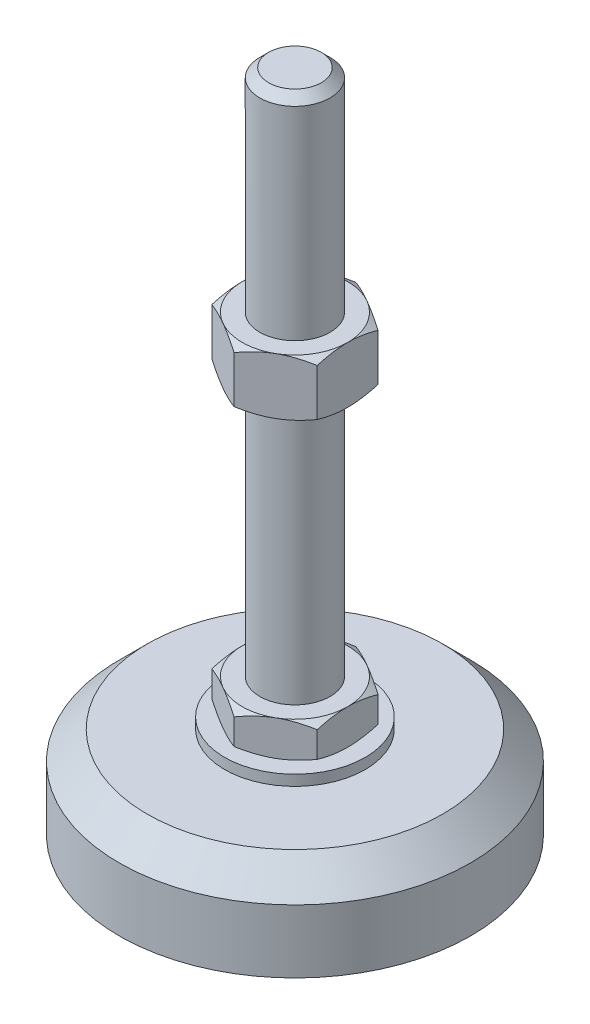
SolidWorks part; units mm, degrees
ref_plane "Спереди" through (0, 0, 0) normal (0, 0, 1) x (1, 0, 0)
ref_plane "Сверху" through (0, 0, 0) normal (0, 1, 0) x (1, 0, 0)
ref_plane "Справа" through (0, 0, 0) normal (1, 0, 0) x (0, 0, -1)
sketch "Эскиз1" plane through (0, 0, 0) normal (0, 0, 1) x (1, 0, 0)
  line L0 (0, 0) -> (-50, 0)
  line L3 (-50, 0) -> (-50, 18)
  line L5 (-20, 29) -> (-10, 29)
  line L12 (-10, 39) -> (-10, 186.5)
  line L13 (-10, 186.5) -> (-7.5, 189)
  line L14 (-7.5, 189) -> (0, 189)
  line L15 (0, 189) -> (0, 0) construction
  line L16 (-10, 29) -> (0, 29) construction
  line L17 (0, 0) -> (0, 189)
  line L18 (0, 0) -> (0, -7.9595) construction
  line L19 (-10, 39) -> (-10, 29)
  line L20 (-20, 29) -> (-20, 26)
  line L21 (-20, 26) -> (-42, 26)
  line L22 (-42, 26) -> (-50, 18)
  point P8 (-10, 112.75)
  point P23 (-15, 29)
  dimension "D1" = 20
  dimension "D2" = 29
  dimension "D3" = 10
  dimension "D4" = 100
  dimension "D5" = 10
  dimension "D6" = 2.5
  dimension "D7" = 45
  dimension "D8" = 40
  dimension "D10" = 150
  dimension "D11" = 18
  dimension "D12" = 45
  dimension "D13" = 3
revolve "Повернуть1" add sketch "Эскиз1" angle 360 about L17
sketch "Эскиз2" plane through (0, 29, 0) normal (0, 1, 0) x (1, 0, 0)
  line L1 (0, 17.3205) -> (-15, 8.6603)
  line L2 (-15, 8.6603) -> (-15, -8.6603)
  line L3 (-15, -8.6603) -> (0, -17.3205)
  line L4 (0, -17.3205) -> (15, -8.6603)
  line L5 (15, -8.6603) -> (15, 8.6603)
  line L6 (15, 8.6603) -> (0, 17.3205)
  circle A0 centre (0, 0) radius 15 construction
  dimension "D1" = 30
extrude "Бобышка-Вытянуть1" add sketch "Эскиз2" along normal up to vertex (10 mm away) up to point (-10, 39, 0)
ref_plane "Плоскость1" through (0, 112.75, 0) normal (0, 1, 0) x (1, 0, 0)
sketch "Эскиз3" plane through (0, 112.75, 0) normal (0, 1, 0) x (1, 0, 0)
  line L6 (15, 8.6603) -> (0, 17.3205)
  line L7 (0, 17.3205) -> (-15, 8.6603)
  line L8 (-15, 8.6603) -> (-15, -8.6603)
  line L9 (-15, -8.6603) -> (0, -17.3205)
  line L10 (0, -17.3205) -> (15, -8.6603)
  line L11 (15, -8.6603) -> (15, 8.6603)
  line L12 (15, 8.6603) -> (0, 17.3205)
  line L13 (0, 17.3205) -> (-15, 8.6603)
  line L14 (-15, 8.6603) -> (-15, -8.6603)
  line L15 (-15, -8.6603) -> (0, -17.3205)
  line L16 (0, -17.3205) -> (15, -8.6603)
  line L17 (15, -8.6603) -> (15, 8.6603)
  dimension "D1" = 0
extrude "Бобышка-Вытянуть2" add sketch "Эскиз3" along normal blind 16
sketch "Эскиз4" plane through (0, 0, 0) normal (0, 0, 1) x (1, 0, 0)
  line L0 (-15, 128.75) -> (-28.8564, 120.75)
  line L1 (-28.8564, 120.75) -> (-28.8564, 128.75)
  line L2 (-28.8564, 128.75) -> (-15, 128.75)
  line L3 (-28.8564, 120.75) -> (-15, 112.75)
  line L4 (50, 112.75) -> (-50, 112.75) construction
  line L5 (-15, 112.75) -> (-28.8564, 112.75)
  line L6 (-28.8564, 112.75) -> (-28.8564, 120.75)
  line L7 (-15, 128.75) -> (-15, 112.75) construction
  line L8 (-15, 39) -> (-23.6603, 39)
  line L9 (-23.6603, 39) -> (-23.6603, 34)
  line L10 (-23.6603, 34) -> (-15, 39)
  line L11 (-15, 29) -> (-23.6603, 34)
  line L12 (-23.6603, 34) -> (-23.6603, 29)
  line L13 (-23.6603, 29) -> (-15, 29)
  line L14 (0, 189) -> (0, 96.3793) construction
  dimension "D1" = 30
  dimension "D2" = 30
revolve "Вырез-Повернуть2" cut sketch "Эскиз4" angle 360 about L14
